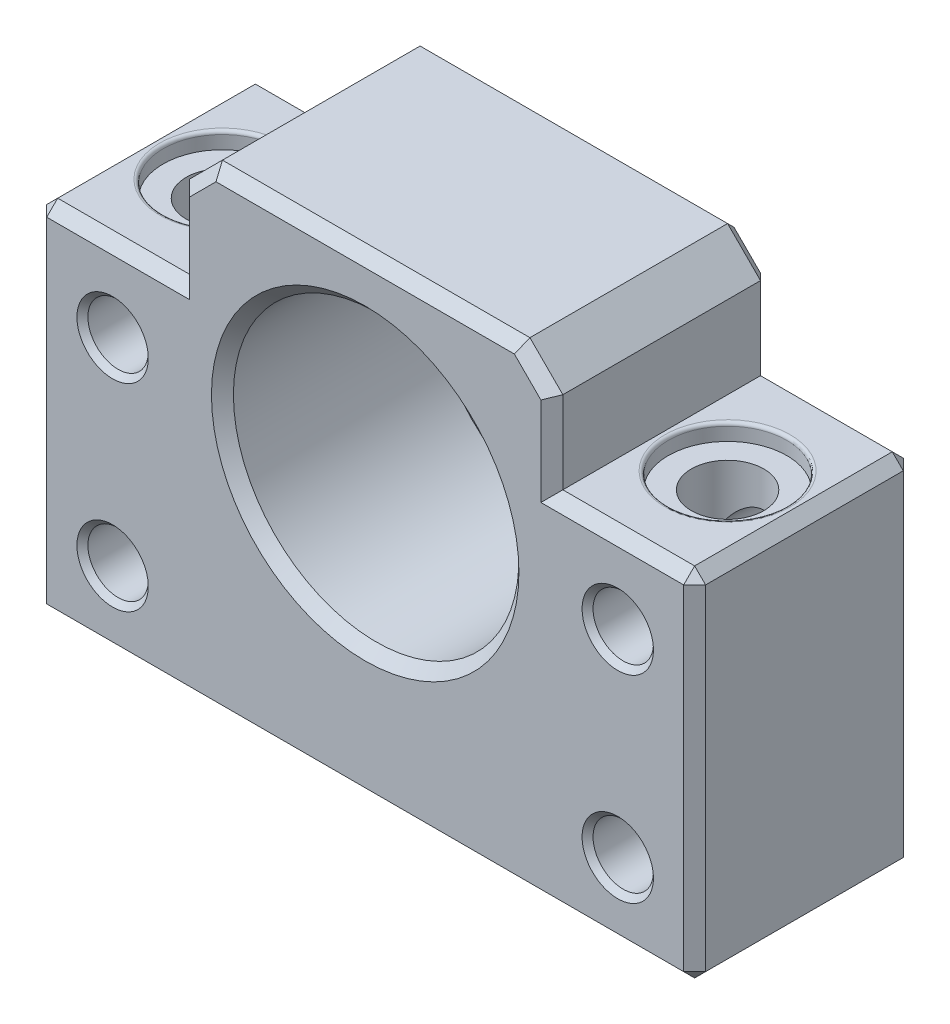
SolidWorks part; units mm, degrees
material "1060 Alloy"
ref_plane "Front Plane" through (0, 0, 0) normal (0, 0, 1) x (1, 0, 0)
ref_plane "Top Plane" through (0, 0, 0) normal (0, 1, 0) x (1, 0, 0)
ref_plane "Right Plane" through (0, 0, 0) normal (1, 0, 0) x (0, 0, -1)
sketch "Sketch1" plane through (0, 0, 0) normal (0, 0, 1) x (1, 0, 0)
  line L0 (-17, 0) -> (-17, -43) construction
  line L1 (0, 0) -> (-30, 0) construction
  line L2 (0, 0) -> (0, -43) construction
  line L3 (0, -43) -> (-30, -43) construction
  line L4 (-30, 0) -> (-30, -43) construction
  line L5 (-30, -10.5) -> (0, -10.5) construction
  line L6 (17, 0) -> (-17, 0)
  line L7 (-17, 0) -> (-17, -10.5)
  line L8 (-17, -10.5) -> (-30, -10.5)
  line L9 (-30, -10.5) -> (-30, -43)
  line L10 (-30, -43) -> (30, -43)
  line L11 (30, -10.5) -> (30, -43)
  line L12 (17, -10.5) -> (30, -10.5)
  line L13 (17, 0) -> (17, -10.5)
  circle A0 centre (0, -18) radius 13 construction
  circle A1 centre (0, -18) radius 13
  dimension "D6" = 26
  dimension "D1" = 43
  dimension "D2" = 30
  dimension "D3" = 17
  dimension "D4" = 32.5
  dimension "D5" = 25
extrude "Boss-Extrude1" add sketch "Sketch1" along normal blind 20
chamfer "Chamfer1" distance 3 angle 45 2 edges at (17, 0, 10) (-17, 0, 10)
chamfer "Chamfer2" distance 1 angle 45 26 edges at (0, -43, 0) (-30, -43, 10) (-30, -26.75, 0) (0, -43, 20) (30, -43, 10) (30, -26.75, 0) (17, -6.75, 0) (15.5, -1.5, 0) (0, 0, 0) (-15.5, -1.5, 0) (-17, -6.75, 0) (-23.5, -10.5, 0) (-30, -10.5, 10) (23.5, -10.5, 0) (30, -10.5, 10) (30, -26.75, 20) (23.5, -10.5, 20) (17, -6.75, 20) (15.5, -1.5, 20) (0, 0, 20) (-15.5, -1.5, 20) (-17, -6.75, 20) (-23.5, -10.5, 20) (-30, -26.75, 20) (13, -18, 20) (13, -18, 0)
sketch "Sketch2" plane through (0, 0, 0) normal (0, 0, -1) x (-1, 0, 0)
  line L0 (0, 0) -> (0, -43) construction
  line L1 (29, -43) -> (-29, -43) construction
  line L2 (-23, -27) -> (23, -27) construction
  line L3 (-23, -18) -> (23, -18) construction
  line L4 (-23, -18) -> (-23, -36) construction
  line L5 (-23, -36) -> (23, -36) construction
  line L6 (23, -18) -> (23, -36) construction
  line L7 (-23, -18) -> (23, -36) construction
  line L8 (-23, -36) -> (23, -18) construction
  circle A0 centre (-23, -18) radius 2.75
  circle A1 centre (23, -18) radius 2.75
  circle A2 centre (23, -36) radius 2.75
  circle A3 centre (-23, -36) radius 2.75
  point P5 (0, -27)
  dimension "D1" = 5.5
  dimension "D2" = 46
  dimension "D3" = 18
  dimension "D4" = 25
extrude "Cut-Extrude1" cut sketch "Sketch2" against normal through all
sketch "Sketch3" plane through (0, -43, 0) normal (0, -1, 0) x (1, 0, 0)
  line L0 (0, 0) -> (0, 20) construction
  line L1 (-29, 20) -> (29, 20) construction
  line L3 (23, 10) -> (-23, 10) construction
  circle A0 centre (23, 10) radius 3.3
  circle A1 centre (-23, 10) radius 3.3
  point P5 (0, 10)
  dimension "D1" = 6.6
  dimension "D2" = 46
extrude "Cut-Extrude2" cut sketch "Sketch3" against normal up to next
sketch "Sketch4" plane through (0, -10.5, 0) normal (0, 1, 0) x (1, 0, 0)
  line L0 (0, -20) -> (0, 0) construction
  line L1 (13.5858, -20) -> (-13.5858, -20) construction
  line L2 (30, -10) -> (-30, -10) construction
  line L3 (30, -1) -> (30, -19) construction
  line L4 (-30, -19) -> (-30, -1) construction
  circle A0 centre (23, -10) radius 5.4
  circle A1 centre (-23, -10) radius 5.4
  dimension "D1" = 10.8
extrude "Cut-Extrude3" cut sketch "Sketch4" against normal blind 1.5
chamfer "Chamfer3" distance 0.5 angle 45 10 edges at (26.3, -43, 10) (-26.3, -43, 10) (-25.75, -36, 20) (-20.25, -18, 20) (25.75, -36, 20) (20.25, -18, 20) (-20.25, -18, 0) (-25.75, -36, 0) (25.75, -36, 0) (20.25, -18, 0)
fillet "Fillet1" radius 0.3 2 edges at (17.6, -10.5, 10) (-17.6, -10.5, 10)
